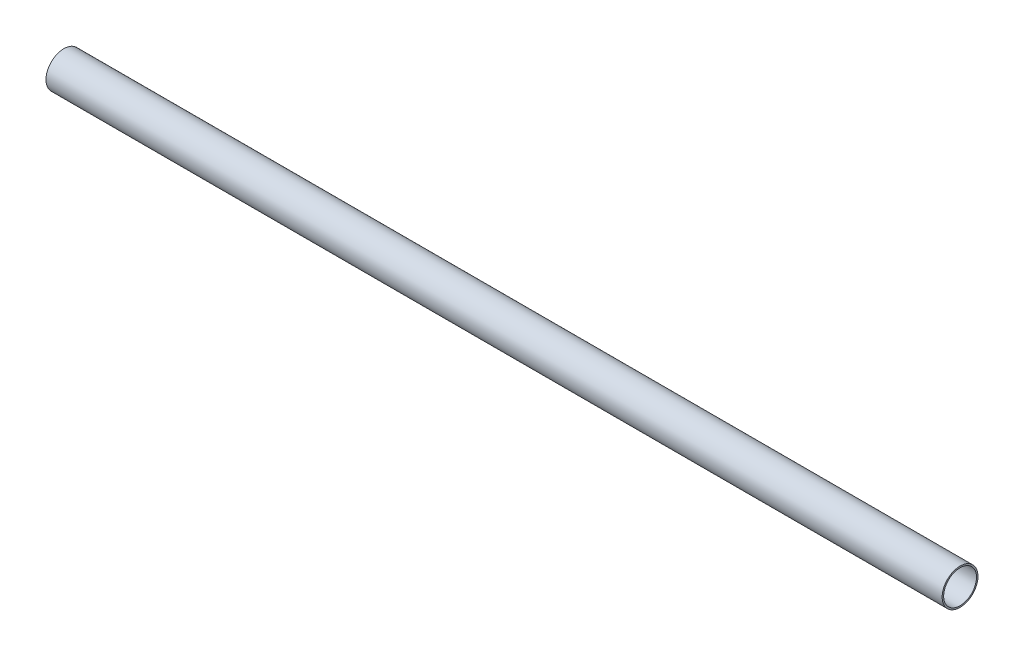
SolidWorks part; units mm, degrees
material "Hexcel AS4C (3000 丝)"
ref_plane "前视基准面" through (0, 0, 0) normal (0, 0, 1) x (1, 0, 0)
ref_plane "上视基准面" through (0, 0, 0) normal (0, 1, 0) x (1, 0, 0)
ref_plane "右视基准面" through (0, 0, 0) normal (1, 0, 0) x (0, 0, -1)
sketch "草图1" plane through (0, 0, 0) normal (0, 0, 1) x (1, 0, 0)
  line L0 (-450, 5.961) -> (-450, 5.461)
  line L1 (-450, 5.461) -> (-150, 5.461)
  line L2 (-150, 5.461) -> (-150, 5.961)
  line L3 (-150, 5.961) -> (-450, 5.961)
  line L4 (-450, -0.039) -> (0, -0.039) construction
  line L5 (-150, 5.461) -> (-150, -0.039) construction
revolve "旋转1" add sketch "草图1" angle 360 about L4
